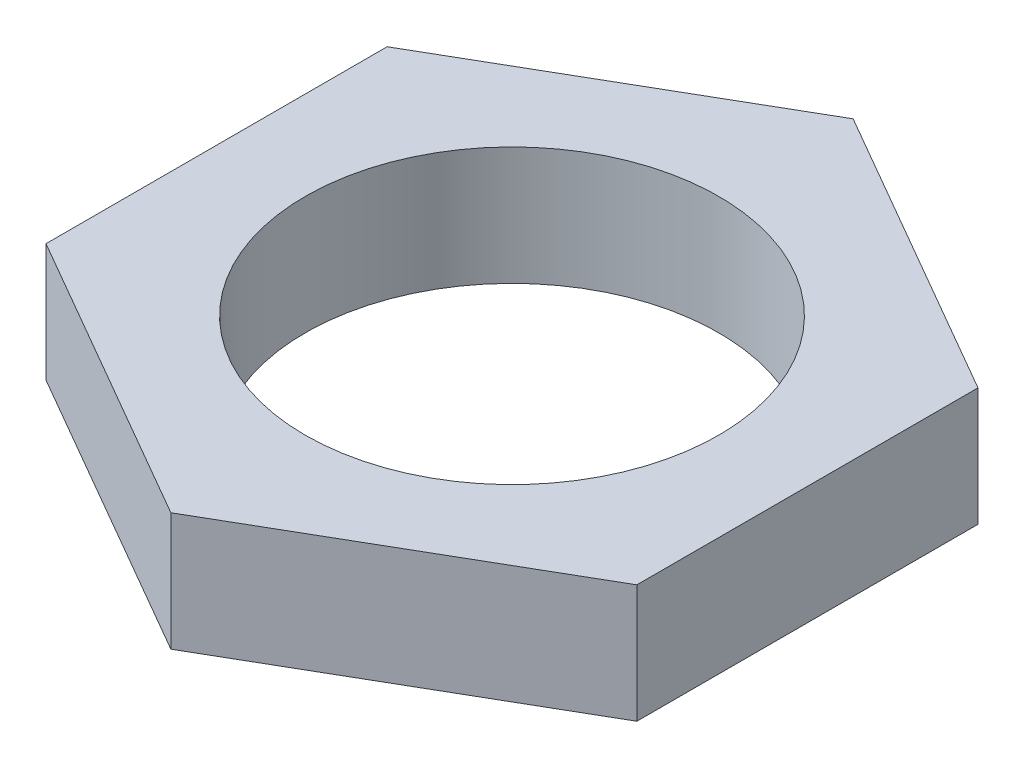
SolidWorks part; units mm, degrees
ref_plane "Front Plane" through (0, 0, 0) normal (0, 0, 1) x (1, 0, 0)
ref_plane "Top Plane" through (0, 0, 0) normal (0, 1, 0) x (1, 0, 0)
ref_plane "Right Plane" through (0, 0, 0) normal (1, 0, 0) x (0, 0, -1)
sketch "Sketch1" plane through (0, 0, 0) normal (0, 1, 0) x (1, 0, 0)
  line L1 (0, 27.4963) -> (-23.8125, 13.7482)
  line L2 (-23.8125, 13.7482) -> (-23.8125, -13.7482)
  line L3 (-23.8125, -13.7482) -> (0, -27.4963)
  line L4 (0, -27.4963) -> (23.8125, -13.7482)
  line L5 (23.8125, -13.7482) -> (23.8125, 13.7482)
  line L6 (23.8125, 13.7482) -> (0, 27.4963)
  circle A0 centre (0, 0) radius 23.8125 construction
  circle A1 centre (0, 0) radius 16.6687
  dimension "D2" = 33.3375
  dimension "D1" = 47.625
extrude "Boss-Extrude1" add sketch "Sketch1" along normal mid plane 9.525
